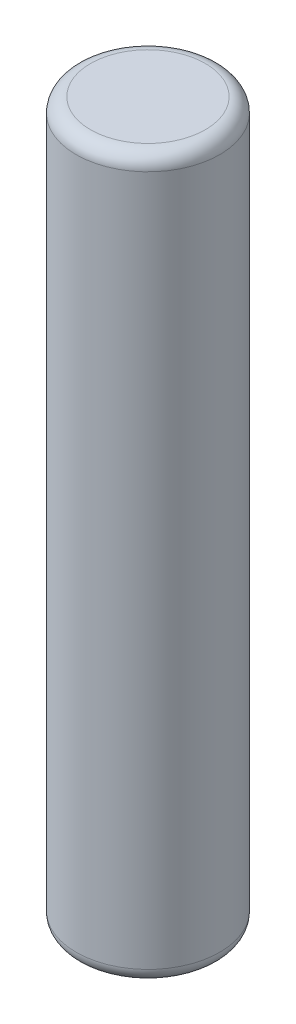
SolidWorks part; units mm, degrees
ref_plane "Front Plane" through (0, 0, 0) normal (0, 0, 1) x (1, 0, 0)
ref_plane "Top Plane" through (0, 0, 0) normal (0, 1, 0) x (1, 0, 0)
ref_plane "Right Plane" through (0, 0, 0) normal (1, 0, 0) x (0, 0, -1)
sketch "Sketch1" plane through (0, 0, 0) normal (0, 1, 0) x (1, 0, 0)
  circle A0 centre (0, 0) radius 4.99
extrude "Boss-Extrude1" add sketch "Sketch1" along normal blind 50
fillet "Fillet1" radius 1 2 edges at (0, 0, 4.99) (0, 50, 4.99)
